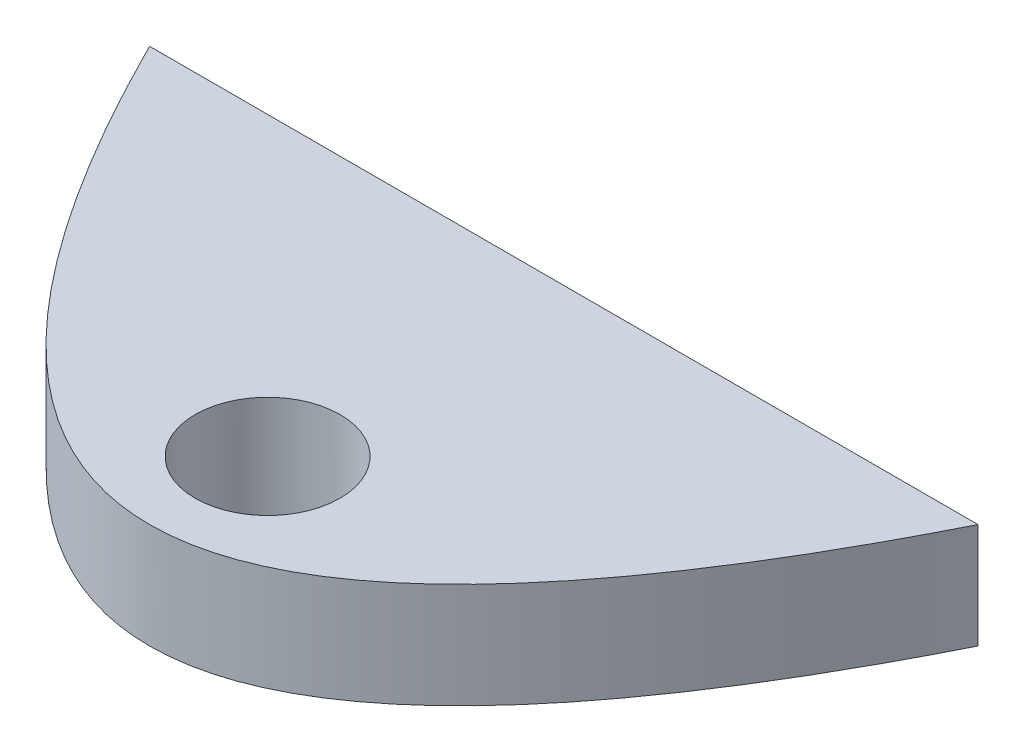
SolidWorks part; units mm, degrees
material "Custom Plastic (2)"
ref_plane "Front Plane" through (0, 0, 0) normal (0, 0, 1) x (1, 0, 0)
ref_plane "Top Plane" through (0, 0, 0) normal (0, 1, 0) x (1, 0, 0)
ref_plane "Right Plane" through (0, 0, 0) normal (1, 0, 0) x (0, 0, -1)
sketch "Sketch1" plane through (0, 0, 0) normal (0, 1, 0) x (1, 0, 0)
  line L0 (-200, 0) -> (200, 0)
  spline S0 degree 2 poles (-225.2396, 53.6645) (0, -453.6645) (225.2396, 53.6645) knots 0 0 0 1 1 1 construction
  spline S1 degree 2 poles (-200, 0) (0, -400) (200, 0) knots 0.056028 0.056028 0.056028 0.943972 0.943972 0.943972
extrude "Boss-Extrude1" add sketch "Sketch1" along normal blind 300
sketch "Sketch2" plane through (0, 300, 0) normal (0, 1, 0) x (1, 0, 0)
  line L0 (0, 200) -> (0, -200)
  line L2 (200, 0) -> (-200, 0) construction
  circle A0 centre (0, -143) radius 35
  parabola Q0 (-200, 0) -> (200, 0) focus (0, -150) apex (0, -200) construction
  point P4 (0, 0)
  dimension "D1" = 70
  dimension "D2" = 143
ref_plane "Plane1" through (0, 150, 0) normal (0, 1, 0) x (1, 0, 0)
sketch "Sketch3" plane through (0, 150, 0) normal (0, 1, 0) x (1, 0, 0)
  circle A0 centre (0, -143) radius 15.5
  dimension "D1" = 31
extrude "Cut-Extrude1" cut sketch "Sketch3" against normal blind 23 and the other way blind 23
ref_plane "Plane2" through (0, 173, 0) normal (0, 1, 0) x (1, 0, 0)
sketch "Sketch4" plane through (0, 173, 0) normal (0, 1, 0) x (1, 0, 0)
  circle A0 centre (0, -143) radius 35
extrude "Cut-Extrude3" cut sketch "Sketch4" along normal blind 300 contours A0
mirror "Mirror1" about plane through (0, 150, 0) normal (0, 1, 0) of "Cut-Extrude3"
sketch "Sketch5" plane through (0, 0, 0) normal (0, 0, -1) x (-1, 0, 0)
  line L0 (-200, 300) -> (200, 300) construction
  line L1 (-245.9193, 355.1493) -> (264.4425, 355.1493)
  line L2 (-245.9193, 355.1493) -> (-245.9193, 96.8)
  line L3 (-245.9193, 96.8) -> (264.4425, 96.8)
  line L4 (264.4425, 355.1493) -> (264.4425, 96.8)
  line L6 (-250.7938, 46) -> (261.0303, 46)
  line L7 (-250.7938, 46) -> (-250.7938, -24.193)
  line L8 (-250.7938, -24.193) -> (261.0303, -24.193)
  line L9 (261.0303, 46) -> (261.0303, -24.193)
  dimension "D1" = 203.2
  dimension "D2" = 254
extrude "Cut-Extrude4" cut sketch "Sketch5" against normal through all
